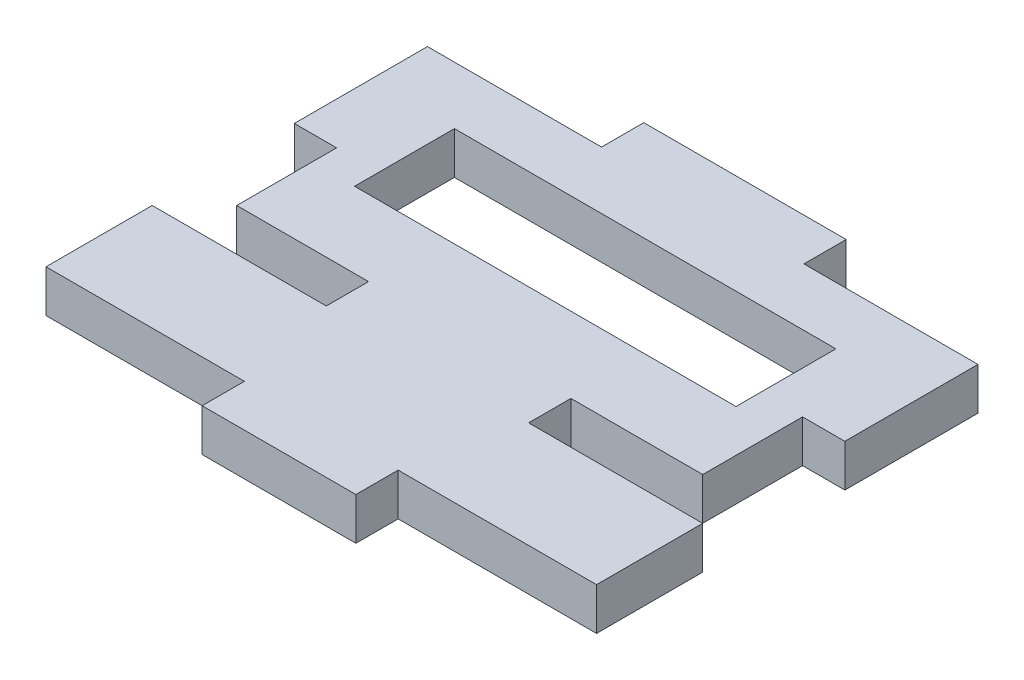
SolidWorks part; units mm, degrees
ref_plane "Front Plane" through (0, 0, 0) normal (0, 0, 1) x (1, 0, 0)
ref_plane "Top Plane" through (0, 0, 0) normal (0, 1, 0) x (1, 0, 0)
ref_plane "Right Plane" through (0, 0, 0) normal (1, 0, 0) x (0, 0, -1)
sketch "Sketch1" plane through (0, 0, 0) normal (0, 1, 0) x (1, 0, 0)
  line L1 (0, 0) -> (41.35, 0)
  line L2 (0, 0) -> (0, 35)
  line L3 (0, 35) -> (41.35, 35)
  line L4 (41.35, 0) -> (41.35, 35)
  dimension "D1" = 35
  dimension "D2" = 41.35
extrude "Boss-Extrude1" add sketch "Sketch1" along normal blind 3.175
sketch "Sketch2" plane through (0, 3.175, 0) normal (0, 1, 0) x (1, 0, 0)
  line L0 (0, 35) -> (0, 0) construction
  line L1 (35, 27.5) -> (6.35, 27.5)
  line L2 (35, 27.5) -> (35, 20)
  line L3 (35, 20) -> (6.35, 20)
  line L4 (6.35, 27.5) -> (6.35, 20)
  line L5 (41.35, 0) -> (41.35, 35) construction
  line L7 (0, 0) -> (41.35, 0) construction
  line L8 (41.35, 11.15) -> (38.175, 11.15) construction
  line L10 (0, 35) -> (13.075, 35)
  line L11 (0, 35) -> (0, 31.825)
  line L12 (0, 31.825) -> (13.075, 31.825)
  line L13 (13.075, 35) -> (13.075, 31.825)
  line L14 (28.275, 31.825) -> (41.35, 31.825)
  line L15 (28.275, 31.825) -> (28.275, 35)
  line L16 (28.275, 35) -> (41.35, 35)
  line L17 (38.175, 21.825) -> (41.35, 21.825)
  line L18 (3.175, 21.825) -> (3.175, 14.325)
  line L19 (38.175, 21.825) -> (38.175, 14.325)
  line L20 (41.35, 21.825) -> (41.35, 11.15)
  line L21 (3.175, 11.15) -> (0, 11.15) construction
  line L22 (3.175, 21.825) -> (0, 21.825)
  line L23 (3.175, 14.325) -> (13.075, 14.325)
  line L24 (38.175, 14.325) -> (28.275, 14.325)
  line L25 (0, 21.825) -> (0, 11.15)
  line L26 (41.35, 31.825) -> (41.35, 35)
  line L27 (13.075, 14.325) -> (13.075, 11.15)
  line L28 (0, 11.15) -> (41.35, 11.15) construction
  line L29 (13.075, 11.15) -> (0, 11.15)
  line L30 (28.275, 14.325) -> (28.275, 11.15)
  line L31 (28.275, 11.15) -> (41.35, 11.15)
  line L33 (41.35, 0) -> (26.45, 0)
  line L34 (41.35, 0) -> (41.35, 3.175)
  line L35 (41.35, 3.175) -> (26.45, 3.175)
  line L36 (26.45, 0) -> (26.45, 3.175)
  line L37 (14.9, 3.175) -> (0, 3.175)
  line L38 (14.9, 3.175) -> (14.9, 0)
  line L39 (14.9, 0) -> (0, 0)
  line L40 (0, 3.175) -> (0, 0)
  point P16 (0, 0)
  point P17 (0, 0)
  point P22 (0, 0)
  point P23 (0, 0)
  point P44 (0, 0)
  point P48 (0, 0)
  point P65 (0, 0)
  point P66 (0, 0)
  dimension "D1" = 3.175
  dimension "D2" = 14.9
  dimension "D3" = 3.175
  dimension "D4" = 20
  dimension "D5" = 13.075
  dimension "D6" = 3.175
  dimension "D7" = 13.075
extrude "Cut-Extrude1" cut sketch "Sketch2" against normal through all
